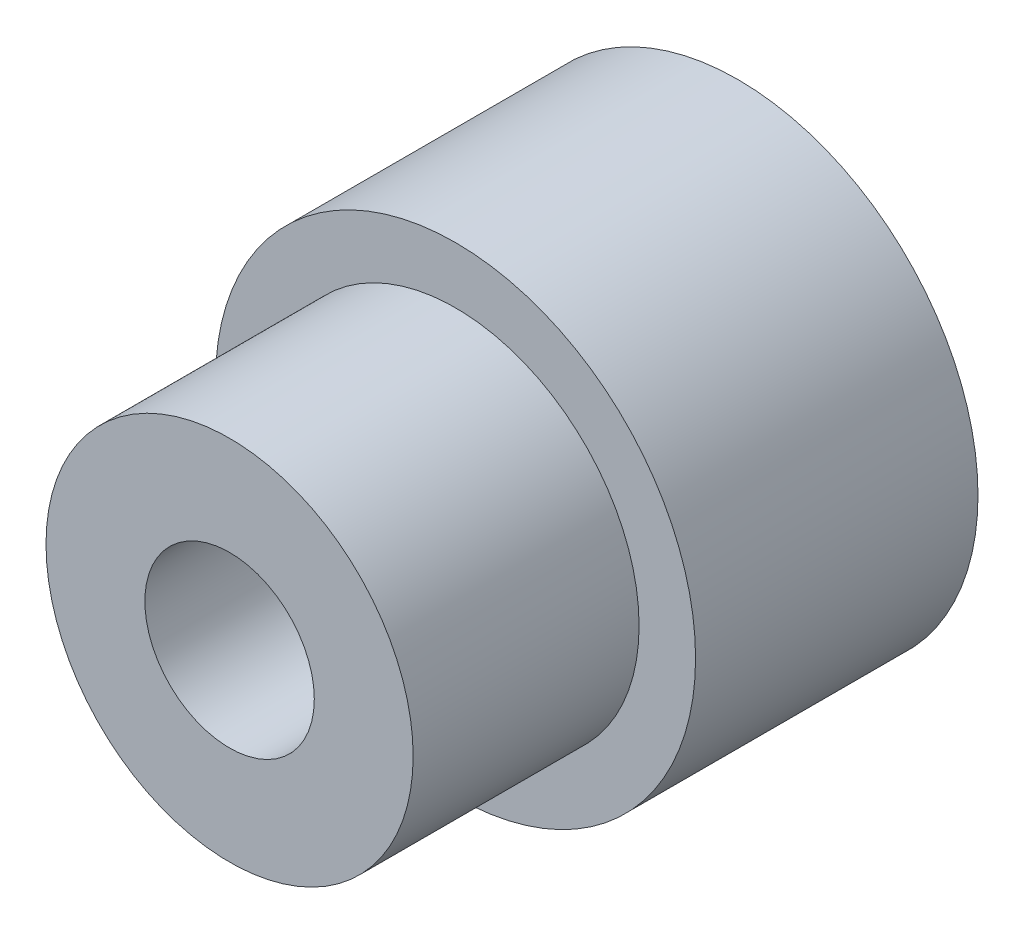
SolidWorks part; units mm, degrees
ref_plane "前视基准面" through (0, 0, 0) normal (0, 0, 1) x (1, 0, 0)
ref_plane "上视基准面" through (0, 0, 0) normal (0, 1, 0) x (1, 0, 0)
ref_plane "右视基准面" through (0, 0, 0) normal (1, 0, 0) x (0, 0, -1)
sketch "草图1" plane through (0, 0, 0) normal (0, 0, 1) x (1, 0, 0)
  circle A0 centre (0, 0) radius 8.5
  dimension "D1" = 17
extrude "凸台-拉伸1" add sketch "草图1" along normal blind 10
sketch "草图2" plane through (0, 0, 10) normal (0, 0, 1) x (1, 0, 0)
  circle A0 centre (0, 0) radius 6.5
  dimension "D1" = 13
extrude "凸台-拉伸2" add sketch "草图2" along normal blind 8
sketch "草图3" plane through (0, 0, 18) normal (0, 0, 1) x (1, 0, 0)
  circle A0 centre (0, 0) radius 3
  dimension "D1" = 6
extrude "切除-拉伸1" cut sketch "草图3" against normal through all
